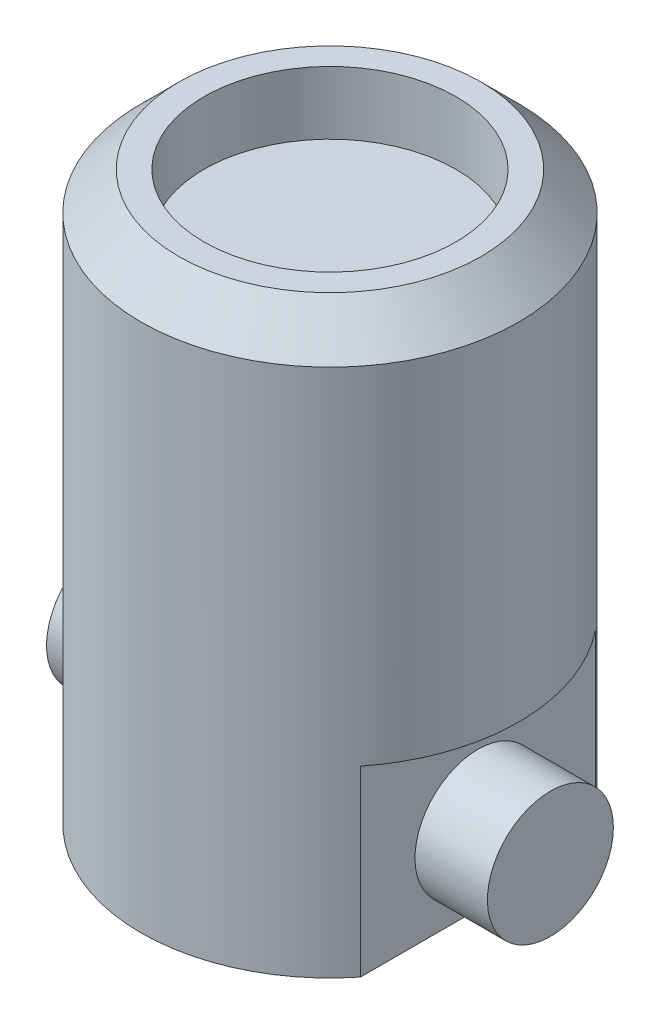
SolidWorks part; units mm, degrees
ref_plane "Front Plane" through (0, 0, 0) normal (0, 0, 1) x (1, 0, 0)
ref_plane "Top Plane" through (0, 0, 0) normal (0, 1, 0) x (1, 0, 0)
ref_plane "Right Plane" through (0, 0, 0) normal (1, 0, 0) x (0, 0, -1)
sketch "Sketch1" plane through (0, 0, 0) normal (0, 1, 0) x (1, 0, 0)
  circle A0 centre (0, 0) radius 30
  dimension "D1" = 60
extrude "Boss-Extrude1" add sketch "Sketch1" along normal blind 90
sketch "Sketch8" plane through (0, 0, 0) normal (0, 0, 1) x (1, 0, 0)
  line L0 (-30, 0) -> (-30, 29)
  line L1 (-30, 90) -> (-30, 0) construction
  line L2 (-30, 29) -> (-23.5, 29)
  line L3 (-23.5, 29) -> (-23.5, 0)
  line L4 (-30, 0) -> (30, 0) construction
  line L5 (-23.5, 0) -> (23.5, 0)
  line L6 (23.5, 0) -> (23.5, 29)
  line L7 (23.5, 29) -> (30, 29)
  line L8 (30, 0) -> (30, 90) construction
  line L9 (30, 29) -> (30, 0)
  line L10 (30, 0) -> (23.5, 0)
  line L11 (-23.5, 0) -> (-30, 0)
  point P5 (0, 0)
  dimension "D1" = 6.5
  dimension "D2" = 6.5
  dimension "D3" = 29
extrude "Cut-Extrude5" cut sketch "Sketch8" against normal mid plane 40 contours L11 L3 L2 L0 | L10 L9 L7 L6
sketch "Sketch5" plane through (0, 0, 0) normal (1, 0, 0) x (0, 0, -1)
  circle A0 centre (0, 12) radius 10
  dimension "D1" = 20
  dimension "D2" = 12
extrude "Boss-Extrude3" add sketch "Sketch5" along normal mid plane 70
sketch "Sketch7" plane through (0, 90, 0) normal (0, 1, 0) x (1, 0, 0)
  circle A0 centre (0, 0) radius 20
  dimension "D1" = 40
extrude "Cut-Extrude4" cut sketch "Sketch7" against normal blind 10
chamfer "Chamfer1" distance 6 angle 45 1 edges at (0, 90, 30)
